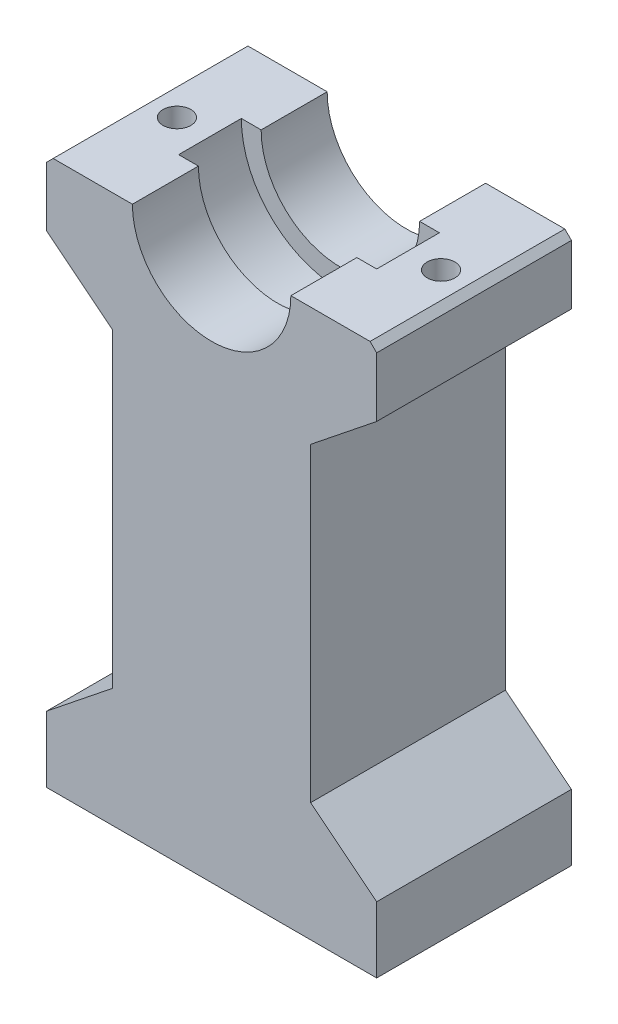
SolidWorks part; units mm, degrees
material "Латунь"
ref_plane "Спереди" through (0, 0, 0) normal (0, 0, 1) x (1, 0, 0)
ref_plane "Сверху" through (0, 0, 0) normal (0, 1, 0) x (1, 0, 0)
ref_plane "Справа" through (0, 0, 0) normal (1, 0, 0) x (0, 0, -1)
sketch "Sketch1" plane through (0, 0, 0) normal (0, 0, 1) x (1, 0, 0)
  line L0 (12, 0) -> (25, 0)
  line L1 (25, 0) -> (25, -10)
  line L2 (25, -83) -> (-25, -83)
  line L3 (-25, -83) -> (-25, -73)
  line L4 (-25, 0) -> (-12, 0)
  line L5 (25, -10) -> (15, -18)
  line L6 (15, -18) -> (15, -65)
  line L7 (15, -65) -> (25, -73)
  line L8 (-25, -10) -> (-15, -18)
  line L9 (-15, -18) -> (-15, -65)
  line L10 (-15, -65) -> (-25, -73)
  line L13 (25, -73) -> (25, -83)
  line L14 (-25, -10) -> (-25, 0)
  arc A0 (-12, 0) -> (12, 0) centre (0, 0) ccw
  point P7 (0, -12)
  dimension "D7" = 50
  dimension "D6" = 12
  dimension "D1" = 8
  dimension "D2" = 10
  dimension "D3" = 83
  dimension "D4" = 8
  dimension "D5" = 10
  dimension "D8" = 30
extrude "Boss-Extrude1" add sketch "Sketch1" along normal blind 29.5
sketch "Sketch2" plane through (0, -83, 0) normal (0, -1, 0) x (1, 0, 0)
  line L0 (-25, 14.75) -> (25, 14.75) construction
  line L1 (-25, 29.5) -> (-25, 0) construction
  line L2 (25, 29.5) -> (25, 0) construction
  line L4 (-10, 12.275) -> (10, 12.275)
  line L5 (-10, 12.275) -> (-10, 17.225) construction
  line L6 (-10, 17.225) -> (10, 17.225)
  line L7 (10, 12.275) -> (10, 17.225) construction
  line L8 (-10, 12.275) -> (10, 17.225) construction
  line L9 (-10, 17.225) -> (10, 12.275) construction
  arc A0 (-10, 17.225) -> (-10, 12.275) centre (-10, 14.75) ccw
  arc A1 (10, 17.225) -> (10, 12.275) centre (10, 14.75) cw
  point P6 (0, 14.75)
  point P7 (0, 14.75)
extrude "Boss-Extrude2" add sketch "Sketch2" along normal blind 7
chamfer "Chamfer1" distance 0.5 angle 45 4 edges at (0, -90, 12.275) (-12.475, -90, 14.75) (0, -90, 17.225) (12.475, -90, 14.75)
sketch "Sketch3" plane through (0, -83, 0) normal (0, -1, 0) x (1, 0, 0)
  line L0 (-25, 14.75) -> (25, 14.75) construction
  line L1 (-25, 29.5) -> (-25, 0) construction
  line L2 (25, 29.5) -> (25, 0) construction
  line L3 (-10, 12.275) -> (10, 12.275) construction
  line L4 (10, 17.225) -> (-10, 17.225) construction
  line L5 (-25, 29.5) -> (25, 29.5) construction
  line L6 (0, 17.225) -> (0, 29.5) construction
  line L7 (-10, 17.225) -> (10, 17.225) construction
  line L9 (0, 12.275) -> (0, 0) construction
  point P6 (0, 12.275)
  point P7 (0, 17.225)
  point P22 (0, 23.3625)
  point P23 (0, 6.1375)
hole_wizard "Отверстие обработанное метчиком M5x0.82" positions "Sketch7" profile "Sketch8" tap size "M5x0.8" standard "Ansi Metric"
sketch "Sketch7" plane through (0, -83, 0) normal (0, -1, 0) x (-1, 0, 0)
  line L0 (0, -17.225) -> (0, -29.5) construction
  line L1 (0, -12.275) -> (0, 0) construction
  point P0 (0, -23.3625)
  point P4 (0, -6.1375)
sketch "Sketch8" plane through (0, -83, 23.3625) normal (1, 0, 0) x (0, 0, -1)
  line L0 (0, 0) -> (0, 20.2618)
  line L1 (0, 20.2618) -> (2.1, 19)
  line L2 (2.1, 19) -> (2.1, 0)
  line L5 (2.1, 0) -> (0, 0)
  line L10 (0, 20.2618) -> (-2.1, 19) construction
  line L11 (0, -6.35) -> (0, 107.95) construction
  dimension "Tap Drill Dia." = 4.2
  dimension "Tap Drill Depth" = 19
  dimension "Drill Angle" = 118
cosmetic thread "Hole Thread1" parameters "D1"=15, "D2"=5
cosmetic thread "Hole Thread2" parameters "D1"=15, "D2"=5
sketch "Sketch13" plane through (0, 0, 0) normal (0, 1, 0) x (1, 0, 0)
  line L1 (-15, -10) -> (-6.3248, -10)
  line L2 (-15, -10) -> (-15, -19.5)
  line L3 (-15, -19.5) -> (-6.3248, -19.5)
  line L4 (-6.3248, -10) -> (-6.3248, -19.5)
  line L5 (0, 0) -> (0, -29.5) construction
  line L6 (-12, -29.5) -> (12, -29.5) construction
  point P4 (-6.3248, -14.75)
  point P6 (0, -14.75)
  dimension "D1" = 9.5
  dimension "D4" = 15
revolve "Cut-Revolve1" cut sketch "Sketch13" angle 360 about L5
sketch "Sketch10" plane through (0, 0, 0) normal (0, 1, 0) x (1, 0, 0)
  line L1 (-15, -19.5) -> (-15, -10) construction
  line L3 (15, -10) -> (15, -19.5) construction
  line L4 (-25, -14.75) -> (-15, -14.75) construction
  line L5 (15, -14.75) -> (25, -14.75) construction
  line L11 (-25, -29.5) -> (-25, 0) construction
  line L12 (25, -29.5) -> (25, 0) construction
  point P14 (-20, -14.75)
  point P17 (20, -14.75)
hole_wizard "Отверстие обработанное метчиком M5x0.81" positions "Sketch12" profile "Sketch11" tap size "M5x0.8" standard "Ansi Metric"
sketch "Sketch12" plane through (0, 0, 0) normal (0, 1, 0) x (1, 0, 0)
  point P0 (-20, -14.75)
  point P3 (20, -14.75)
cosmetic thread "Hole Thread3" parameters "D2"=5
cosmetic thread "Hole Thread4" parameters "D2"=5
sketch "Sketch11" plane through (-20, 0, 14.75) normal (1, 0, 0) x (0, 0, 1)
  line L0 (0, 0) -> (0, 14)
  line L1 (0, 14) -> (2.1, 14)
  line L2 (2.1, 14) -> (2.1, 0)
  line L5 (2.1, 0) -> (0, 0)
  line L11 (0, -6.35) -> (0, 107.95) construction
  dimension "Диаметр проходного сверла" = 4.2
  dimension "Глубина проходного сверла" = 14
chamfer "Фаска1" distance 1 angle 45 2 edges at (25, 0, 14.75) (-25, 0, 14.75)
